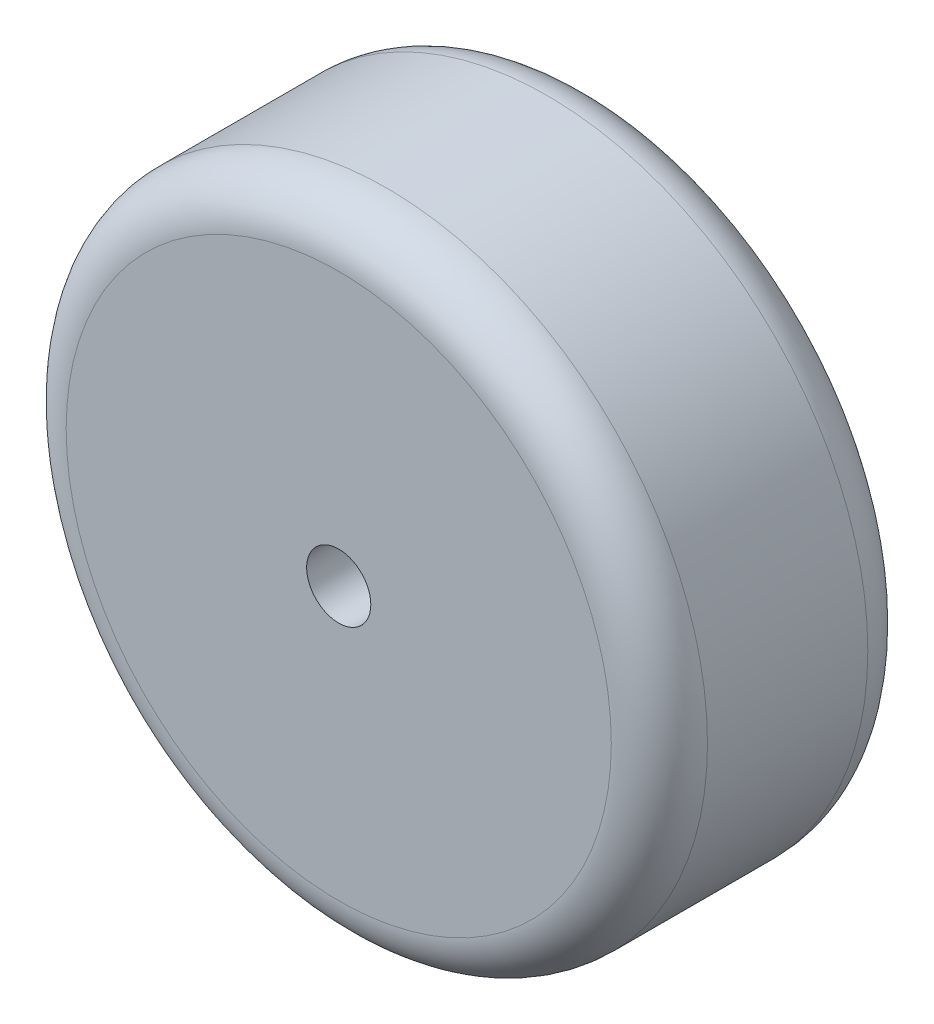
SolidWorks part; units mm, degrees
material "Caucho natural"
ref_plane "Alzado" through (0, 0, 0) normal (0, 0, 1) x (1, 0, 0)
ref_plane "Planta" through (0, 0, 0) normal (0, 1, 0) x (1, 0, 0)
ref_plane "Vista lateral" through (0, 0, 0) normal (1, 0, 0) x (0, 0, -1)
sketch "Croquis1" plane through (0, 0, 0) normal (0, 0, 1) x (1, 0, 0)
  circle A0 centre (0, 0) radius 10
  dimension "D1" = 20
extrude "Saliente-Extruir1" add sketch "Croquis1" along normal blind 8
fillet "Redondeo1" radius 1.5 2 edges at (10, 0, 0) (10, 0, 8)
sketch "Croquis3" plane through (0, 0, 8) normal (0, 0, 1) x (1, 0, 0)
  circle A0 centre (0, 0) radius 1
  dimension "D1" = 2
extrude "Cortar-Extruir1" cut sketch "Croquis3" against normal through all
